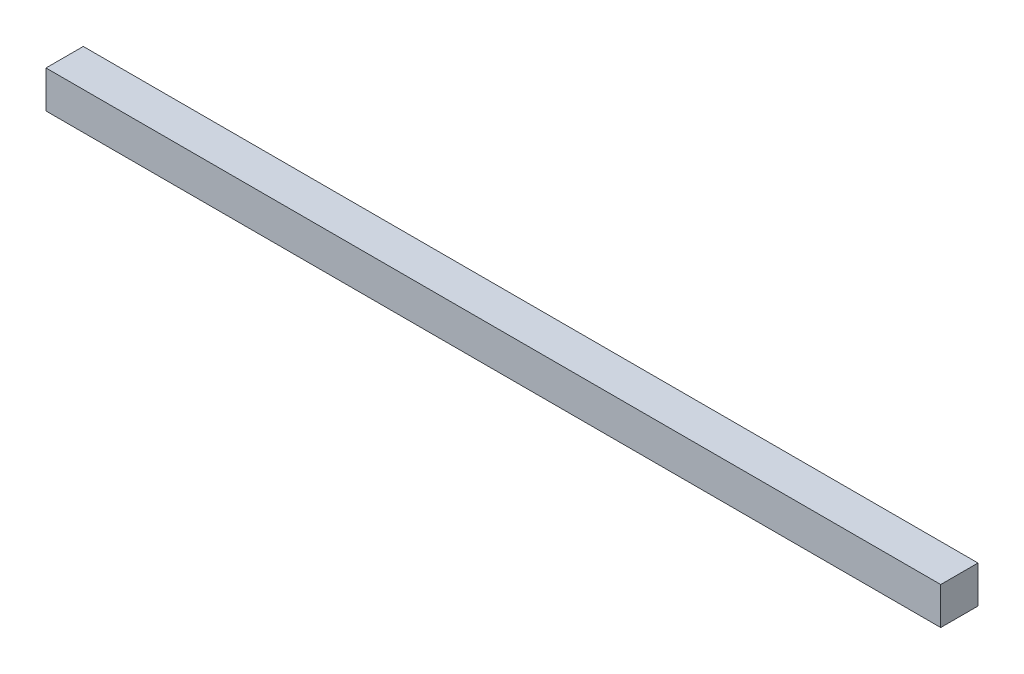
SolidWorks part; units mm, degrees
ref_plane "Front Plane" through (0, 0, 0) normal (0, 0, 1) x (1, 0, 0)
ref_plane "Top Plane" through (0, 0, 0) normal (0, 1, 0) x (1, 0, 0)
ref_plane "Right Plane" through (0, 0, 0) normal (1, 0, 0) x (0, 0, -1)
sketch "Sketch1" plane through (0, 0, 0) normal (0, 1, 0) x (1, 0, 0)
  line L1 (-46.949, 20.9848) -> (562.651, 20.9848)
  line L2 (-46.949, 20.9848) -> (-46.949, -4.4152)
  line L3 (-46.949, -4.4152) -> (562.651, -4.4152)
  line L4 (562.651, 20.9848) -> (562.651, -4.4152)
  dimension "D1" = 609.6
  dimension "D2" = 25.4
extrude "Boss-Extrude1" add sketch "Sketch1" along normal blind 25.4
